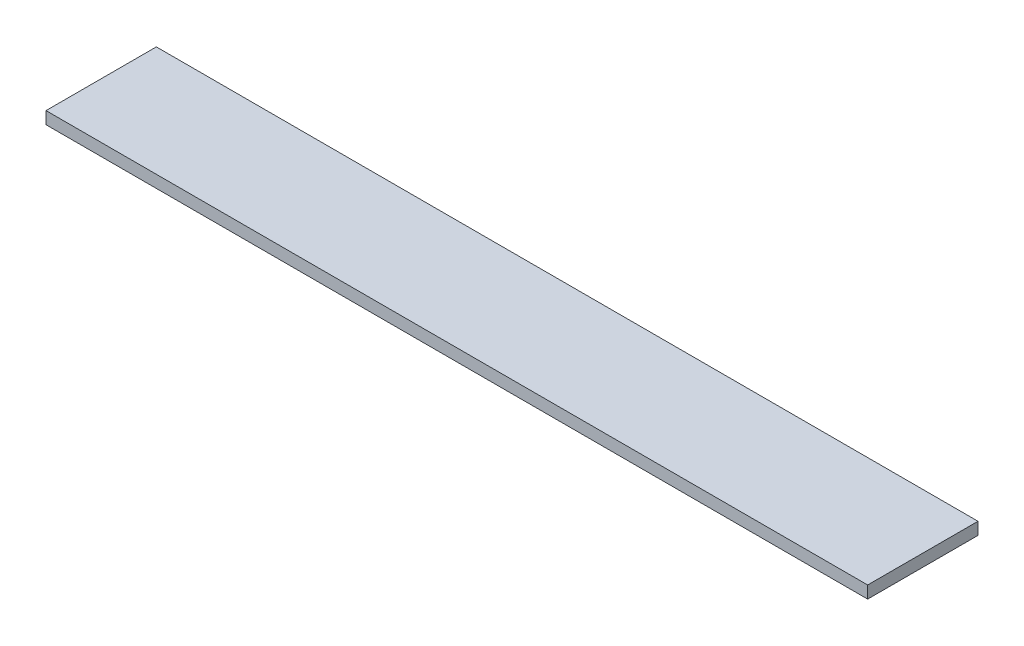
SolidWorks part; units mm, degrees
ref_plane "Front Plane" through (0, 0, 0) normal (0, 0, 1) x (1, 0, 0)
ref_plane "Top Plane" through (0, 0, 0) normal (0, 1, 0) x (1, 0, 0)
ref_plane "Right Plane" through (0, 0, 0) normal (1, 0, 0) x (0, 0, -1)
sketch "Sketch1" plane through (0, 0, 0) normal (0, 1, 0) x (1, 0, 0)
  line L1 (-100.53, 13.5) -> (100.53, 13.5)
  line L2 (-100.53, 13.5) -> (-100.53, -13.5)
  line L3 (-100.53, -13.5) -> (100.53, -13.5)
  line L4 (100.53, 13.5) -> (100.53, -13.5)
  line L5 (-100.53, 13.5) -> (100.53, -13.5) construction
  line L6 (-100.53, -13.5) -> (100.53, 13.5) construction
  point P0 (0, 0)
  dimension "D1" = 27
  dimension "D2" = 201.06
extrude "Boss-Extrude1" add sketch "Sketch1" against normal blind 3
